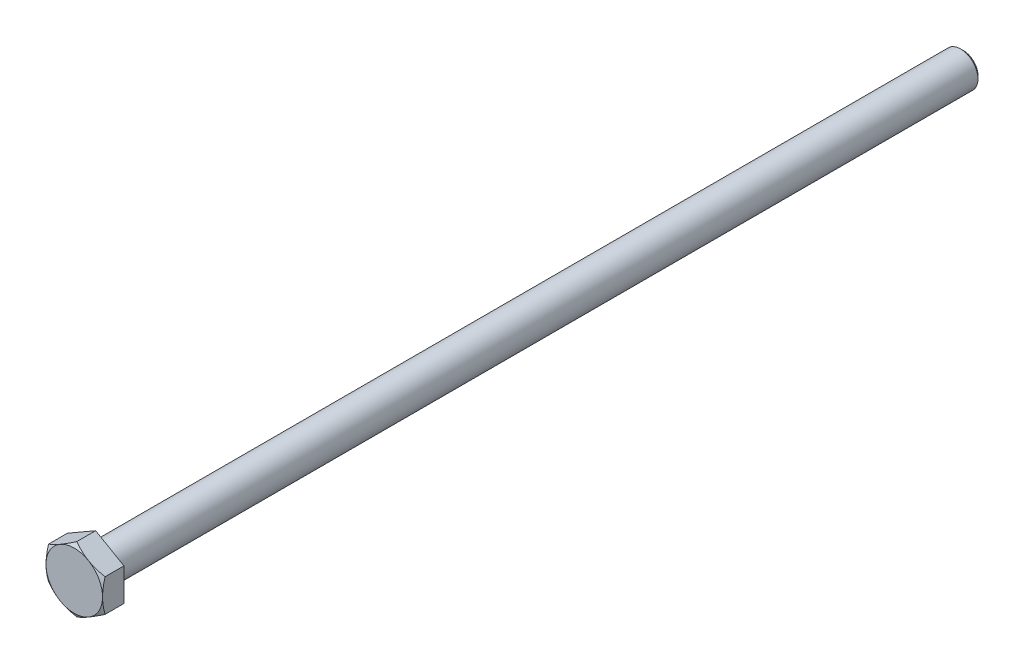
SolidWorks part; units mm, degrees
ref_plane "Front Plane" through (0, 0, 0) normal (0, 0, 1) x (1, 0, 0)
ref_plane "Top Plane" through (0, 0, 0) normal (0, 1, 0) x (1, 0, 0)
ref_plane "Right Plane" through (0, 0, 0) normal (1, 0, 0) x (0, 0, -1)
sketch "Sketch1" plane through (0, 0, 0) normal (0, 0, 1) x (1, 0, 0)
  line L0 (0, 0) -> (0, 5.6465) construction
  line L2 (0, 5.6465) -> (-4.89, 2.8232)
  line L3 (-4.89, 2.8232) -> (-4.89, -2.8232)
  line L4 (-4.89, -2.8232) -> (0, -5.6465)
  line L5 (0, -5.6465) -> (4.89, -2.8232)
  line L6 (4.89, -2.8232) -> (4.89, 2.8232)
  line L7 (4.89, 2.8232) -> (0, 5.6465)
  circle A0 centre (0, 0) radius 4.89 construction
  dimension "HEX" = 9.78
extrude "Boss-Extrude1" add sketch "Sketch1" along normal blind 3.85
sketch "Sketch2" plane through (0, 0, 0) normal (1, 0, 0) x (0, 0, -1)
  line L0 (0, 0) -> (150, 0) construction
  line L1 (0, 0) -> (0, 3.25)
  line L4 (149.5, 3) -> (150, 2.5)
  line L7 (150, 2.5) -> (150, 0)
  line L8 (150, 0) -> (0, 0)
  line L9 (149.5, 3) -> (0.25, 3)
  arc A3 (0.25, 3) -> (0, 3.25) centre (0.25, 3.25) cw
  dimension "D1" = 0.25
  dimension "LENGTH" = 150
  dimension "WIDTH2" = 5
  dimension "WIDTH1" = 6
  dimension "D5" = 45
revolve "Revolve1" add sketch "Sketch2" angle 360 about L0
cosmetic thread "Cosmetic Thread1" parameters "D1"=108, "D2"=6
sketch "Sketch3" plane through (0, 0, 0) normal (1, 0, 0) x (0, 0, -1)
  line L0 (-12.2049, 0) -> (129.7862, 0) construction
  line L1 (-3.85, 5.6465) -> (-3.4132, 5.6465)
  line L2 (-0.15, 5.6465) -> (-0.15, 4.5366)
  line L3 (-3.4132, 5.6465) -> (-3.85, 4.89)
  line L4 (-0.15, 4.5366) -> (0, 4.45)
  line L5 (-3.85, 4.89) -> (-3.85, 5.6465)
  line L6 (0, -2.8232) -> (0, 2.8232) construction
  line L7 (-3.85, 5.6465) -> (0, 5.6465) construction
  line L8 (-3.85, 2.8232) -> (-3.85, 5.6465) construction
  line L10 (0, 4.45) -> (0, 5.6465)
  line L11 (0, 5.6465) -> (-0.15, 5.6465)
  dimension "D1" = 30
  dimension "SAME AS HEX" = 9.78
  dimension "D3" = 30
  dimension "C" = 0.15
  dimension "DW" = 8.9
revolve "Cut-Revolve1" cut sketch "Sketch3" angle 360 about L0
